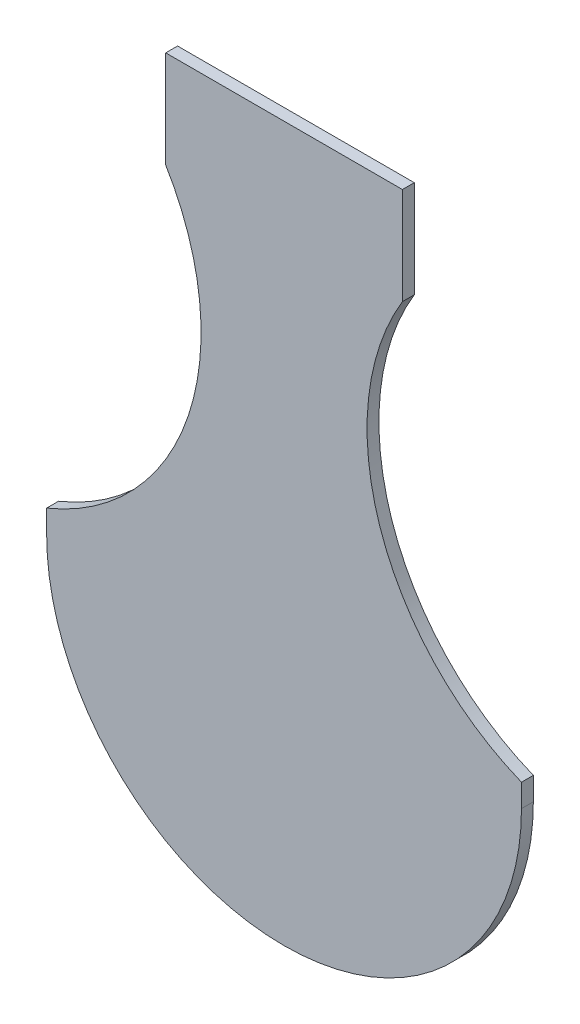
SolidWorks part; units mm, degrees
ref_plane "Front Plane" through (0, 0, 0) normal (0, 0, 1) x (1, 0, 0)
ref_plane "Top Plane" through (0, 0, 0) normal (0, 1, 0) x (1, 0, 0)
ref_plane "Right Plane" through (0, 0, 0) normal (1, 0, 0) x (0, 0, -1)
sketch "Sketch1" plane through (0, 0, 0) normal (0, 0, 1) x (1, 0, 0)
  line L9 (60, 65.7794) -> (60, 0)
  line L10 (60, 0) -> (-60, 0)
  line L11 (0, 0) -> (0, 180.4555) construction
  line L12 (-60, 65.7794) -> (-60, 0)
  line L14 (-29.9097, 155.9087) -> (-29.9097, 180.4555)
  line L15 (29.9097, 155.9087) -> (29.9097, 180.4555)
  line L16 (-29.9097, 180.4555) -> (29.9097, 180.4555)
  line L17 (83.4736, 123.7038) -> (0, 95.8355) construction
  arc A0 (60, 65.7794) -> (29.9097, 155.9087) centre (83.4736, 123.7038) cw
  arc A2 (-60, 65.7794) -> (-29.9097, 155.9087) centre (-83.4736, 123.7038) ccw
  circle A3 centre (0, 95.8355) radius 60 construction
  circle A4 centre (0, 180.4555) radius 24.62 construction
  point P13 (0, 0)
  point P14 (0, 0)
  point P15 (0, 0)
  dimension "D1" = 120
  dimension "D2" = 62.5
  dimension "D6" = 120
  dimension "D7" = 49.24
  dimension "D3" = 29.9097
  dimension "D4" = 83.4736
  dimension "D5" = 59.8193
  dimension "D8" = 24.5468
  dimension "D9" = 24.5468
extrude "Boss-Extrude1" add sketch "Sketch1" along normal blind 3
sketch "Sketch2" plane through (0, 0, 3) normal (0, 0, 1) x (1, 0, 0)
  line L0 (-60, 0) -> (60, 0) construction
  line L1 (60, 0) -> (60, 65.7794) construction
  line L2 (-60, 60) -> (-60, -14.1553)
  line L3 (-60, -14.1553) -> (60, -14.1553)
  line L4 (60, -14.1553) -> (60, 60)
  circle A0 centre (0, 60) radius 60 construction
  arc A1 (60, 60) -> (-60, 60) centre (0, 60) cw
  point P8 (0, 0)
  point P10 (60, -14.1553)
  point P15 (0, 0)
  point P16 (0, 0)
  point P17 (0, 0)
  point P18 (0, 0)
  point P19 (-60, 61.0467)
  dimension "D1" = 120
extrude "Cut-Extrude1" cut sketch "Sketch2" against normal through all
